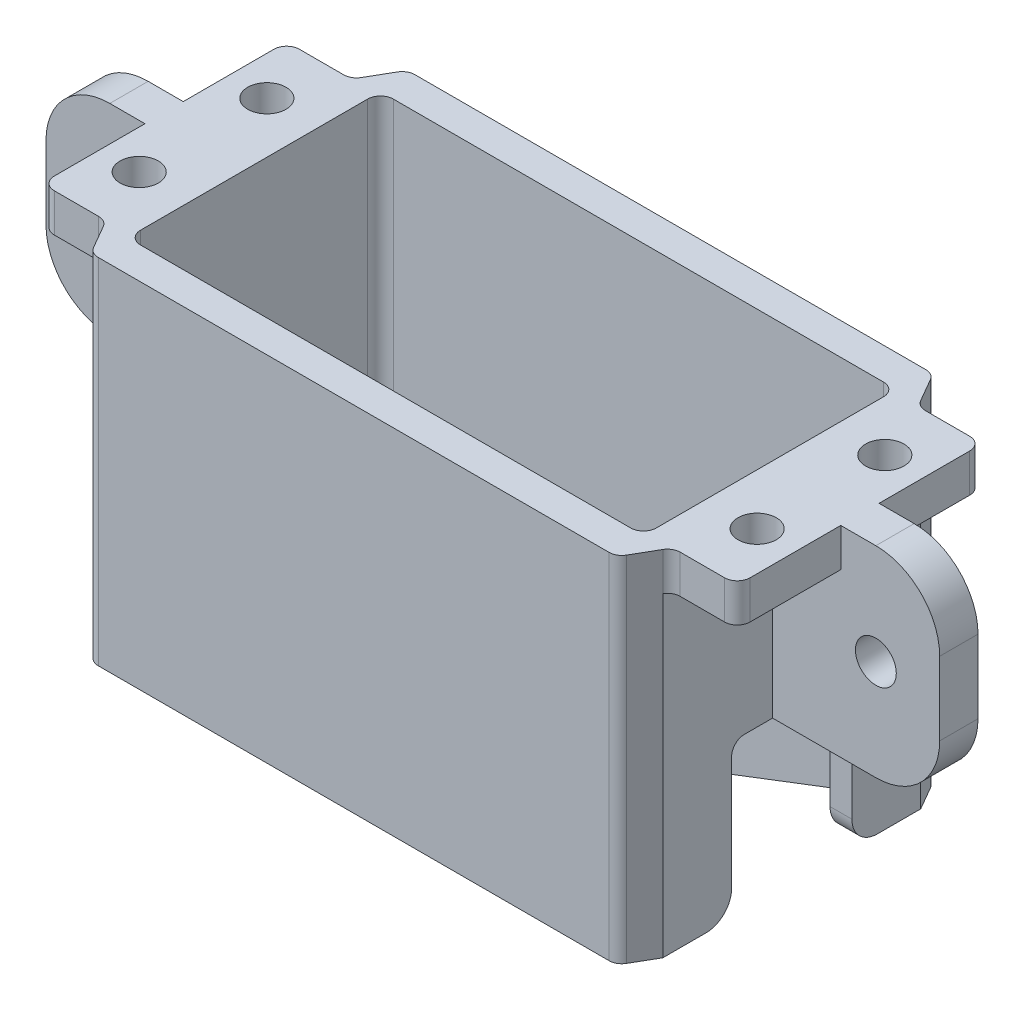
SolidWorks part; units mm, degrees
ref_plane "Piano frontale" through (0, 0, 0) normal (0, 0, 1) x (1, 0, 0)
ref_plane "Piano superiore" through (0, 0, 0) normal (0, 1, 0) x (1, 0, 0)
ref_plane "Piano destro" through (0, 0, 0) normal (1, 0, 0) x (0, 0, -1)
sketch "Schizzo3" plane through (0, -1.8, 0) normal (0, 1, 0) x (1, 0, 0)
  line L20 (27.25, -1.6) -> (27.25, -8.6)
  line L21 (27.25, -1.6) -> (27.25, 1.6)
  line L22 (27.25, 8.6) -> (27.25, 1.6)
  line L23 (22.7774, 9.6) -> (26.25, 9.6)
  line L24 (21.9113, 10.1) -> (20.8721, 11.9)
  line L25 (-20.0061, 12.4) -> (20.0061, 12.4)
  line L26 (-21.9113, 10.1) -> (-20.8721, 11.9)
  line L27 (-26.25, 9.6) -> (-22.7774, 9.6)
  line L28 (-27.25, 1.6) -> (-27.25, 8.6)
  line L29 (-27.25, 1.6) -> (-27.25, -1.6)
  line L30 (-27.25, -8.6) -> (-27.25, -1.6)
  line L31 (-22.7774, -9.6) -> (-26.25, -9.6)
  line L32 (26.25, -9.6) -> (22.7774, -9.6)
  line L34 (-21.9113, -10.1) -> (-20.8721, -11.9)
  line L35 (-20.0061, -12.4) -> (20.0061, -12.4)
  line L36 (21.9113, -10.1) -> (20.8721, -11.9)
  line L38 (-19.2, -9.9) -> (19.2, -9.9)
  line L39 (20.2, -8.9) -> (20.2, 8.9)
  line L40 (-19.2, 9.9) -> (19.2, 9.9)
  line L41 (-20.2, 8.9) -> (-20.2, -8.9)
  arc A14 (27.25, 8.6) -> (26.25, 9.6) centre (26.25, 8.6) ccw
  arc A15 (21.9113, 10.1) -> (22.7774, 9.6) centre (22.7774, 10.6) ccw
  arc A16 (20.8721, 11.9) -> (20.0061, 12.4) centre (20.0061, 11.4) ccw
  arc A17 (-20.0061, 12.4) -> (-20.8721, 11.9) centre (-20.0061, 11.4) ccw
  arc A18 (-22.7774, 9.6) -> (-21.9113, 10.1) centre (-22.7774, 10.6) ccw
  arc A19 (-26.25, 9.6) -> (-27.25, 8.6) centre (-26.25, 8.6) ccw
  arc A20 (-27.25, -8.6) -> (-26.25, -9.6) centre (-26.25, -8.6) ccw
  arc A22 (26.25, -9.6) -> (27.25, -8.6) centre (26.25, -8.6) ccw
  arc A23 (19.2, -9.9) -> (20.2, -8.9) centre (19.2, -8.9) ccw
  arc A24 (-21.9113, -10.1) -> (-22.7774, -9.6) centre (-22.7774, -10.6) ccw
  arc A25 (-20.8721, -11.9) -> (-20.0061, -12.4) centre (-20.0061, -11.4) ccw
  arc A26 (20.0061, -12.4) -> (20.8721, -11.9) centre (20.0061, -11.4) ccw
  arc A27 (22.7774, -9.6) -> (21.9113, -10.1) centre (22.7774, -10.6) ccw
  arc A28 (20.2, 8.9) -> (19.2, 9.9) centre (19.2, 8.9) ccw
  arc A29 (-19.2, 9.9) -> (-20.2, 8.9) centre (-19.2, 8.9) ccw
  arc A30 (-20.2, -8.9) -> (-19.2, -9.9) centre (-19.2, -8.9) ccw
  circle A34 centre (24.2, -5) radius 1.5
  circle A35 centre (24.2, 5) radius 1.5
  circle A36 centre (-24.2, 5) radius 1.5
  circle A37 centre (-24.2, -5) radius 1.5
extrude "Estrusione-Estrusione2" add sketch "Schizzo3" against normal offset from surface (27.7 mm away) 3
sketch "Schizzo4" plane through (27.25, 0, 0) normal (1, 0, 0) x (0, 0, -1)
  line L1 (-3.7102, -17.5388) -> (3.7102, -17.5388)
  line L2 (-4.7102, -18.5388) -> (-4.7102, -30.617)
  line L3 (-3.7102, -31.617) -> (3.7102, -31.617)
  line L4 (4.7102, -18.5388) -> (4.7102, -30.617)
  line L5 (-4.7102, -17.5388) -> (4.7102, -31.617) construction
  line L6 (-4.7102, -31.617) -> (4.7102, -17.5388) construction
  arc A0 (-3.7102, -17.5388) -> (-4.7102, -18.5388) centre (-3.7102, -18.5388) ccw
  arc A1 (-4.7102, -30.617) -> (-3.7102, -31.617) centre (-3.7102, -30.617) ccw
  arc A2 (3.7102, -31.617) -> (4.7102, -30.617) centre (3.7102, -30.617) ccw
  arc A3 (3.7102, -17.5388) -> (4.7102, -18.5388) centre (3.7102, -18.5388) cw
  point P0 (0, -24.5779)
  dimension "D1" = 1
extrude "Taglio-Estrusione1" cut sketch "Schizzo4" against normal up to next
sketch "Schizzo5" plane through (0, -1.8, 0) normal (0, 1, 0) x (1, 0, 0)
  line L0 (27.25, 8.6) -> (27.25, -8.6)
  line L1 (0, 12.4) -> (0, -12.4) construction
  line L7 (20.0061, 12.4) -> (-20.0061, 12.4) construction
  line L8 (-20.0061, -12.4) -> (20.0061, -12.4) construction
  line L17 (21.9113, -9.6) -> (21.9113, 9.6)
  line L19 (22.605, 8.8985) -> (22.605, -8.8985) construction
  line L20 (21.9113, 10.1) -> (20.8721, 11.9) construction
  line L21 (20.8721, -11.9) -> (21.9113, -10.1) construction
  line L22 (21.9113, 10.1) -> (21.9113, -10.1) construction
  line L23 (-21.9113, 10.1) -> (-21.9113, -10.1) construction
  line L25 (21.9113, -9.6) -> (21.9113, -11.3707)
  line L26 (21.9113, -11.3707) -> (27.5074, -11.3707)
  line L27 (27.5074, -11.3707) -> (27.25, -8.6)
  line L28 (21.9113, 9.6) -> (21.9113, 11.6657)
  line L29 (21.9113, 11.6657) -> (27.25, 11.5037)
  line L30 (27.25, 11.5037) -> (27.25, 8.6)
extrude "Taglio-Estrusione2" cut sketch "Schizzo5" against normal up to surface (24.7 mm away) from offset 3 up to face at (4.7925, -29.5, 0) offset against normal yes
mirror "Specchia1" about plane through (0, 0, 0) normal (1, 0, 0) of "Taglio-Estrusione2"
fillet "Raccordo1" radius 2 2 edges at (21.0557, -29.5, 4.7102) (21.0557, -29.5, -4.7102)
sketch "Schizzo6" plane through (0, 0, 0) normal (0, 0, 1) x (1, 0, 0)
  line L0 (21.9113, -17.5388) -> (30, -17.5388)
  line L1 (35, -12.5388) -> (35, -6.8)
  line L2 (30, -1.8) -> (21.9113, -1.8)
  line L3 (21.9113, -1.8) -> (21.9113, -17.5388)
  line L4 (-22.7, -1.8) -> (-25.7, -1.8) construction
  line L5 (21.9113, -29.5) -> (21.9113, -27.5) construction
  line L6 (20.2, -17.5388) -> (21.9113, -17.5388) construction
  line L7 (30, -12.5388) -> (30, -6.8) construction
  line L8 (0, -13.64) -> (0, 13.64) construction
  arc A0 (30, -17.5388) -> (35, -12.5388) centre (30, -12.5388) ccw
  arc A1 (35, -6.8) -> (30, -1.8) centre (30, -6.8) ccw
  circle A2 centre (30, -9.6694) radius 1.6
  point P14 (30, -9.6694)
  dimension "D2" = 5
  dimension "D3" = 3.2
  dimension "D1" = 30
extrude "Estrusione-Estrusione3" add sketch "Schizzo6" along normal mid plane 3
sketch "Schizzo8" plane through (0, 0, -12.4) normal (0, 0, -1) x (-1, 0, 0)
  line L0 (-20.0061, -29.5) -> (-1.7865, -36.4699)
  line L1 (1.7865, -36.4699) -> (20.0061, -29.5)
  line L2 (-20.0061, -29.5) -> (20.0061, -29.5) construction
  line L3 (20.0061, -29.5) -> (20.0061, -1.8) construction
  line L4 (20.0061, -29.5) -> (-20.0061, -29.5)
  line L5 (-20.0061, -1.8) -> (20.0061, -1.8) construction
  arc A0 (-1.7865, -36.4699) -> (1.7865, -36.4699) centre (0, -31.8) ccw
  circle A1 centre (0, -31.8) radius 1.6
  dimension "D1" = 5
  dimension "D2" = 30
extrude "Estrusione-Estrusione4" add sketch "Schizzo8" against normal up to surface (2.5 mm away) up to face at (0, -15.65, -9.9)
mirror "Specchia2" about plane through (0, 0, 0) normal (1, 0, 0) of "Estrusione-Estrusione3"
fillet "Raccordo2" radius 2 1 edges at (-21.9113, -17.5388, 0)
